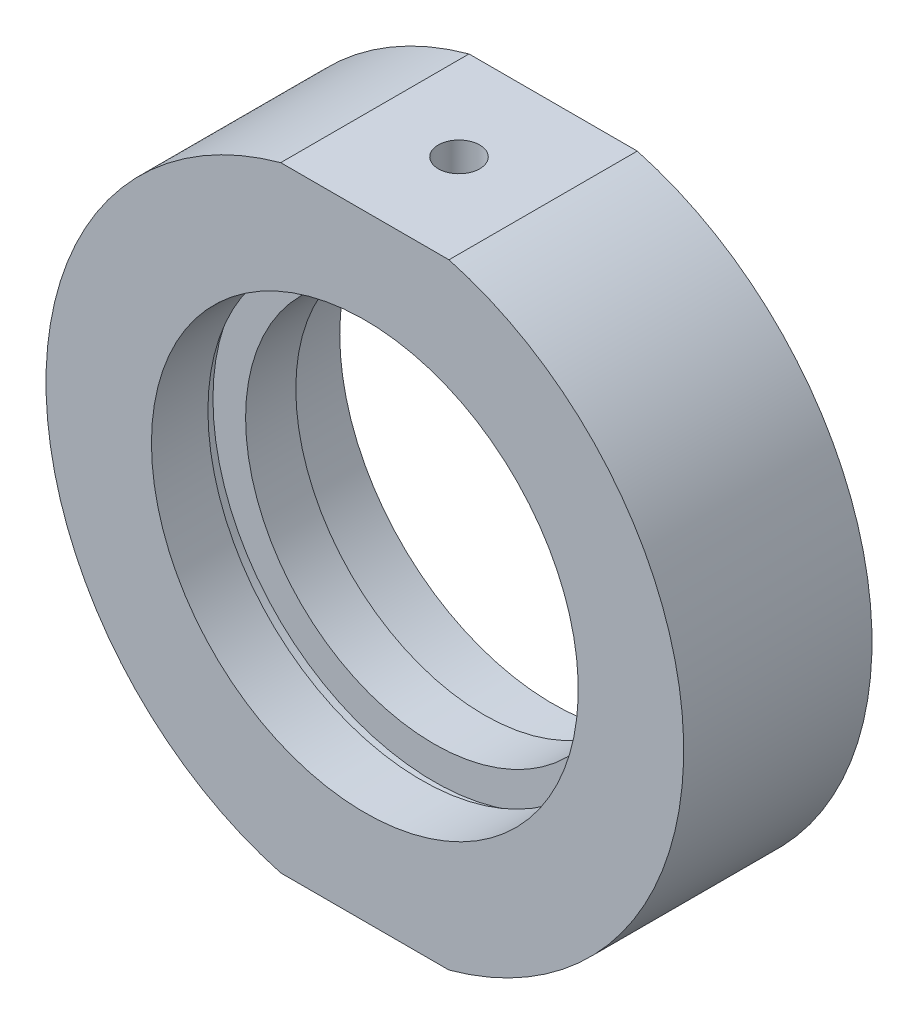
SolidWorks part; units mm, degrees
ref_plane "前视基准面" through (0, 0, 0) normal (0, 0, 1) x (1, 0, 0)
ref_plane "上视基准面" through (0, 0, 0) normal (0, 1, 0) x (1, 0, 0)
ref_plane "右视基准面" through (0, 0, 0) normal (1, 0, 0) x (0, 0, -1)
sketch "草图1" plane through (0, 0, 0) normal (0, 1, 0) x (1, 0, 0)
  line L0 (0, 31.9391) -> (0, -26.491) construction
  line L1 (25.4, 7.5) -> (25.4, -7.5)
  line L3 (17.6, 2) -> (17.6, 3)
  line L4 (17.6, 3) -> (17, 3)
  line L6 (25.4, -7.5) -> (17, -7.5)
  line L7 (17, -7.5) -> (17, -3)
  line L8 (17.6, -2) -> (15, -2)
  line L9 (15, -2) -> (15, 2)
  line L10 (15, 2) -> (17.6, 2)
  line L11 (17, 3) -> (17, 7.5)
  line L12 (17, 7.5) -> (25.4, 7.5)
  line L13 (17.6, -2) -> (17.6, -3)
  line L14 (17.6, -3) -> (17, -3)
  line L17 (35.331, 0) -> (-5.0345, 0) construction
  point P6 (15, 0)
  dimension "D2" = 15
  dimension "D3" = 17
  dimension "D4" = 17
  dimension "D5" = 15
  dimension "D6" = 5.5
  dimension "D7" = 5.5
  dimension "D8" = 17.6
  dimension "D9" = 25.4
  dimension "D10" = 17.6
  dimension "D11" = 1
  dimension "D12" = 1
  dimension "D13" = 7.5
  dimension "D18" = 0
revolve "旋转1" add sketch "草图1" angle 360 about L0
cosmetic thread "装饰螺纹线1" parameters "D2"=35
cosmetic thread "装饰螺纹线2" parameters "D2"=35
sketch "草图2" plane through (0, 0, 7.5) normal (0, 0, 1) x (1, 0, 0)
  line L0 (0, 0) -> (43.1523, 0) construction
  line L1 (-33.152, 33.7489) -> (30.8698, 33.7489)
  line L2 (-33.152, 33.7489) -> (-33.152, 24.5)
  line L3 (-33.152, 24.5) -> (30.8698, 24.5)
  line L4 (30.8698, 33.7489) -> (30.8698, 24.5)
  line L5 (30.8698, -33.7489) -> (30.8698, -24.5)
  line L6 (-33.152, -24.5) -> (30.8698, -24.5)
  line L7 (-33.152, -33.7489) -> (-33.152, -24.5)
  line L8 (-33.152, -33.7489) -> (30.8698, -33.7489)
  dimension "D1" = 24.5
extrude "切除-拉伸1" cut sketch "草图2" against normal blind 49
sketch "草图10" plane through (0, 0, 0) normal (0, 0, 1) x (1, 0, 0)
  line L0 (0, 24.5) -> (0, -24.5)
  line L1 (-6.7015, 24.5) -> (6.7015, 24.5) construction
  line L2 (-6.7015, -24.5) -> (6.7015, -24.5) construction
  line L3 (0, 0) -> (-21.997, 12.7)
  line L4 (0, 0) -> (21.997, 12.7)
  arc A2 (6.7015, -24.5) -> (6.7015, 24.5) centre (0, 0) ccw construction
  arc A3 (-6.7015, 24.5) -> (-6.7015, -24.5) centre (0, 0) ccw construction
  arc A4 (21.997, 12.7) -> (6.7015, 24.5) centre (0, 0) ccw
  arc A5 (-6.7015, 24.5) -> (-21.997, 12.7) centre (0, 0) ccw
  dimension "D1" = 60
  dimension "D2" = 60
hole_wizard "M4 螺纹孔2" positions "草图15" profile "草图16" tap size "M4" standard "ISO"
sketch "草图15" plane through (0, 24.5, 0) normal (0, 1, 0) x (1, 0, 0)
  point P0 (0, 0)
sketch "草图16" plane through (0, 24.5, 0) normal (1, 0, 0) x (0, 0, 1)
  line L0 (0, 0) -> (0, 6.4914)
  line L1 (0, 6.4914) -> (1.65, 5.5)
  line L2 (1.65, 5.5) -> (1.65, 0)
  line L5 (1.65, 0) -> (0, 0)
  line L10 (0, 6.4914) -> (-1.65, 5.5) construction
  line L11 (0, -6.35) -> (0, 107.95) construction
  dimension "螺纹孔钻头直径" = 3.3
  dimension "螺纹孔钻头深度" = 5.5
  dimension "导头角度" = 118
cosmetic thread "孔螺蚊线6" parameters "D1"=5.5, "D2"=4
hole_wizard "M6 螺纹孔2" positions "草图17" profile "草图18" tap size "M6" standard "ISO"
sketch "草图17" plane through (0, -24.5, 0) normal (0, -1, 0) x (-1, 0, 0)
  point P0 (0, 0)
sketch "草图18" plane through (0, -24.5, 0) normal (1, 0, 0) x (0, 0, -1)
  line L0 (0, 0) -> (0, 7.0022)
  line L1 (0, 7.0022) -> (2.5, 5.5)
  line L2 (2.5, 5.5) -> (2.5, 0)
  line L5 (2.5, 0) -> (0, 0)
  line L10 (0, 7.0022) -> (-2.5, 5.5) construction
  line L11 (0, -6.35) -> (0, 107.95) construction
  dimension "螺纹孔钻头直径" = 5
  dimension "螺纹孔钻头深度" = 5.5
  dimension "导头角度" = 118
cosmetic thread "孔螺蚊线7" parameters "D1"=5.5, "D2"=6
